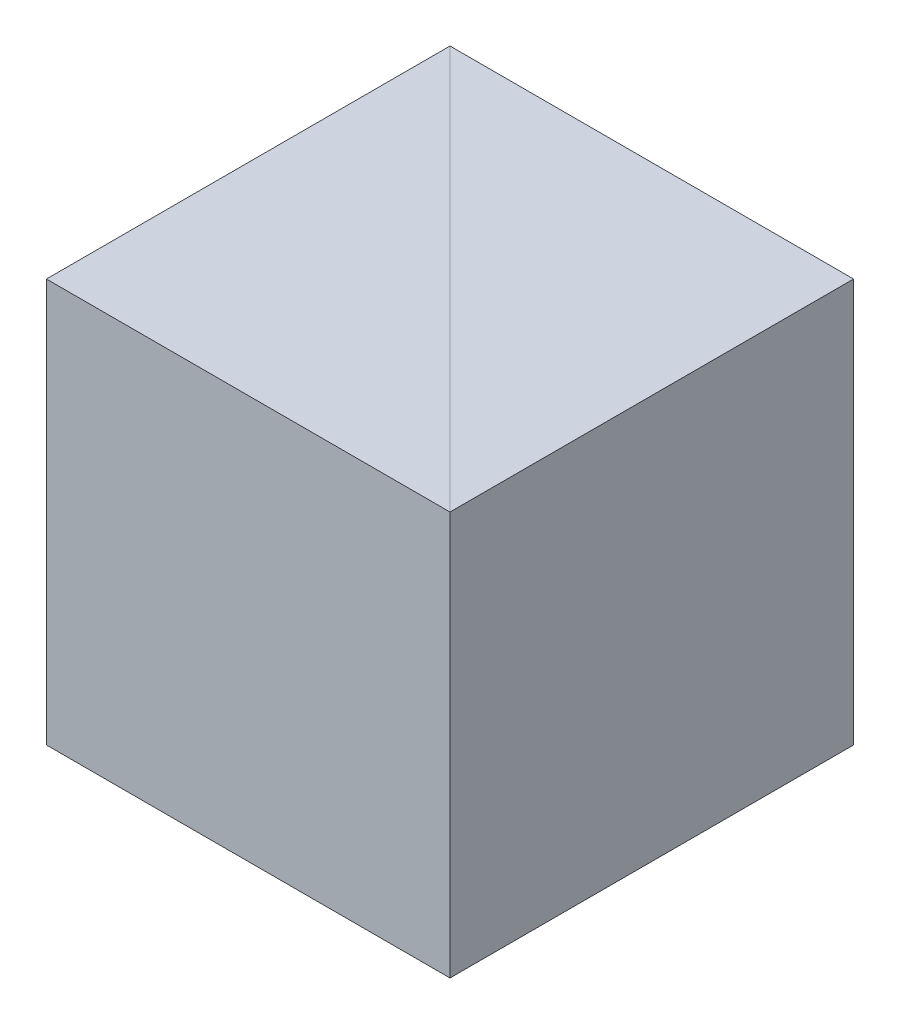
SolidWorks part; units mm, degrees
ref_plane "前视基准面" through (0, 0, 0) normal (0, 0, 1) x (1, 0, 0)
ref_plane "上视基准面" through (0, 0, 0) normal (0, 1, 0) x (1, 0, 0)
ref_plane "右视基准面" through (0, 0, 0) normal (1, 0, 0) x (0, 0, -1)
sketch "草图1" plane through (0, 0, 0) normal (0, 1, 0) x (1, 0, 0)
  line L0 (0, 0) -> (0, 20)
  line L1 (0, 20) -> (-20, 20)
  line L2 (-20, 20) -> (0, 0)
  dimension "D1" = 20
  dimension "D2" = 20
extrude "凸台-拉伸1" add sketch "草图1" along normal blind 20
sketch "草图2" plane through (0, 0, 0) normal (0, -1, 0) x (1, 0, 0)
  line L0 (-20, -20) -> (-20, 0)
  line L1 (-20, 0) -> (0, 0)
  line L2 (0, 0) -> (-20, -20)
extrude "凸台-拉伸2" add sketch "草图2" against normal blind 20 separate body
